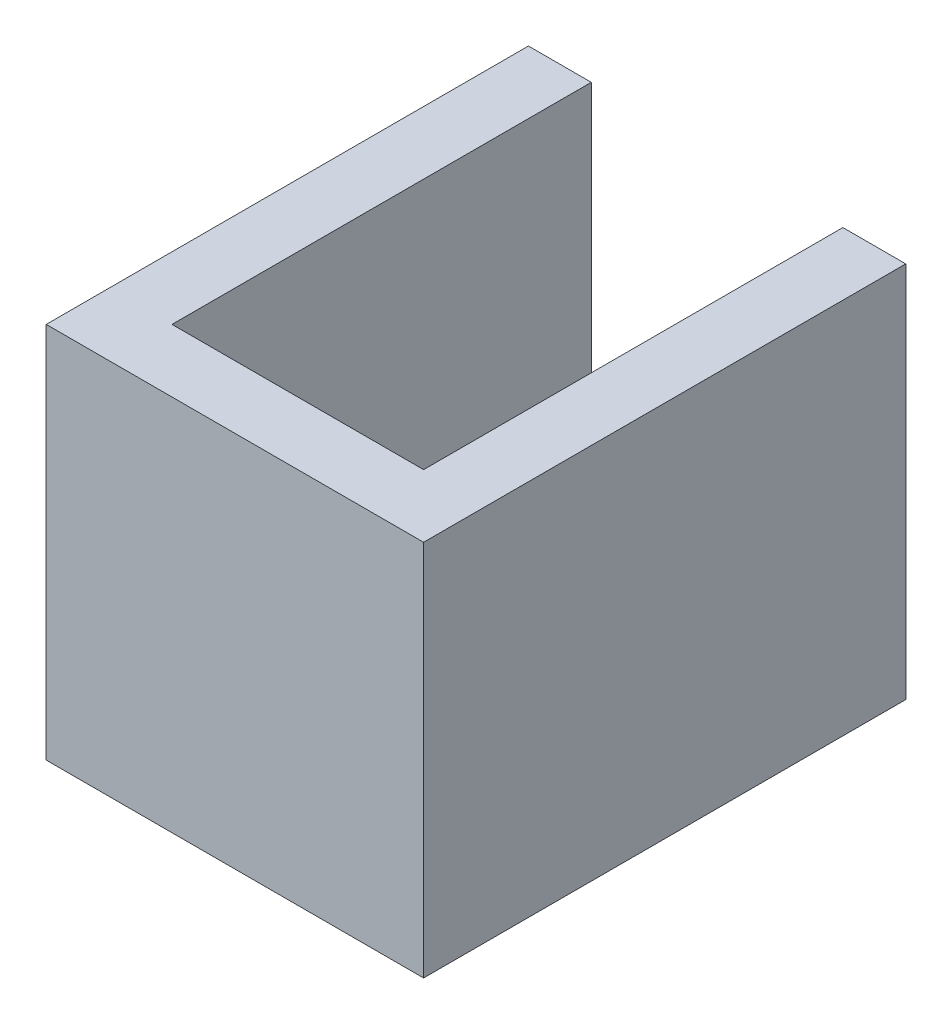
SolidWorks part; units mm, degrees
ref_plane "Front Plane" through (0, 0, 0) normal (0, 0, 1) x (1, 0, 0)
ref_plane "Top Plane" through (0, 0, 0) normal (0, 1, 0) x (1, 0, 0)
ref_plane "Right Plane" through (0, 0, 0) normal (1, 0, 0) x (0, 0, -1)
sketch "Sketch1" plane through (0, 0, 0) normal (0, 1, 0) x (1, 0, 0)
  line L1 (0, 0) -> (18, 0)
  line L2 (0, 0) -> (0, 23)
  line L3 (0, 23) -> (18, 23)
  line L4 (18, 0) -> (18, 23)
  line L5 (3, 3) -> (15, 3)
  line L6 (3, 3) -> (3, 23)
  line L7 (3, 23) -> (15, 23)
  line L8 (15, 3) -> (15, 23)
  dimension "D1" = 20
  dimension "D2" = 12
  dimension "D3" = 3
  dimension "D4" = 3
  dimension "D5" = 3
  dimension "D6" = 0
extrude "Boss-Extrude1" add sketch "Sketch1" along normal blind 18 contours L8 L5 L6 L3 L2 L1 L4
